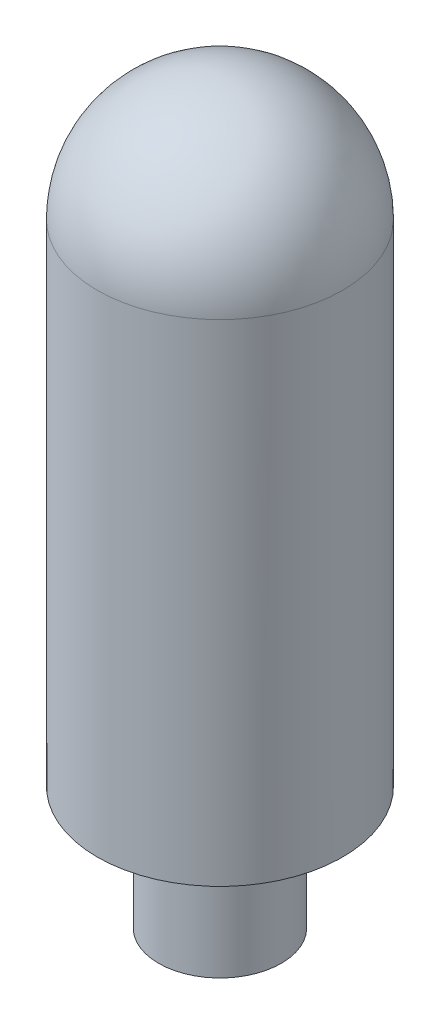
SolidWorks part; units mm, degrees
ref_plane "Front" through (0, 0, 0) normal (0, 0, 1) x (1, 0, 0)
ref_plane "Top" through (0, 0, 0) normal (0, 1, 0) x (1, 0, 0)
ref_plane "Right" through (0, 0, 0) normal (1, 0, 0) x (0, 0, -1)
sketch "Sketch2" plane through (0, 0, 0) normal (0, 0, 1) x (1, 0, 0)
  line L0 (0, 0) -> (2, 0)
  line L1 (2, 0) -> (2, 4)
  line L2 (2, 4) -> (4, 4)
  line L3 (4, 4) -> (4, 20)
  line L4 (0, 34.2935) -> (0, -10.9998) construction
  line L5 (0, 0) -> (0, 24)
  arc A0 (4, 20) -> (0, 24) centre (0, 20) ccw
  dimension "D1" = 2
  dimension "D2" = 4
  dimension "D3" = 4
  dimension "D4" = 20
revolve "Revolve1" add sketch "Sketch2" angle 360 about L4
